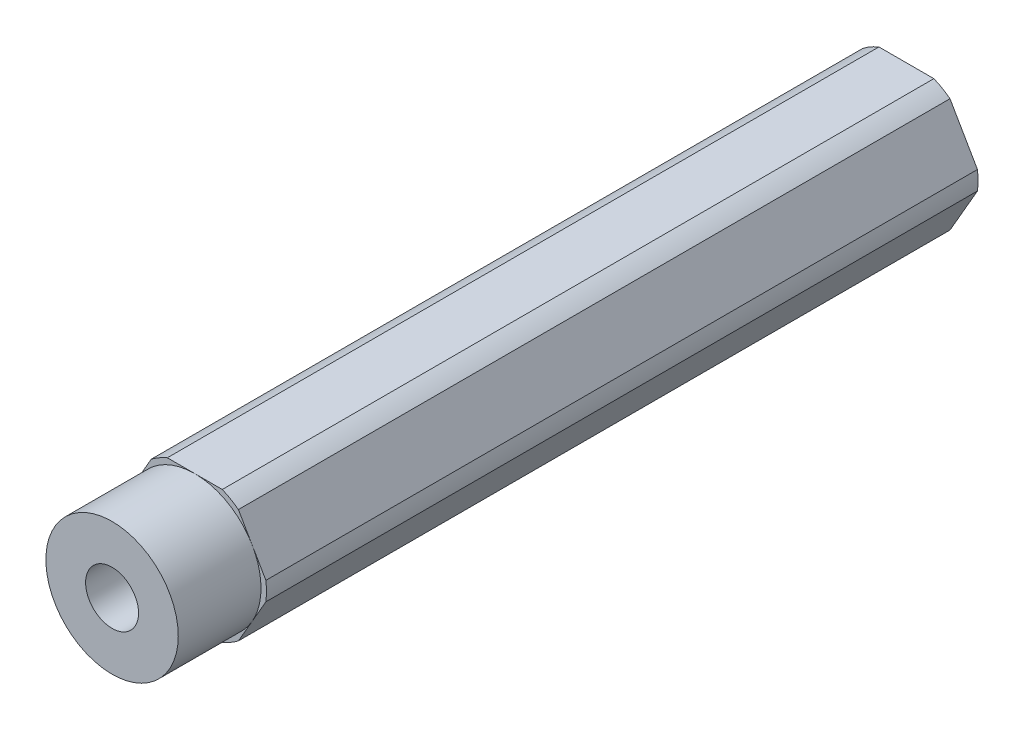
SolidWorks part; units mm, degrees
material "6061-T6 (SS)"
ref_plane "Front Plane" through (0, 0, 0) normal (0, 0, 1) x (1, 0, 0)
ref_plane "Top Plane" through (0, 0, 0) normal (0, 1, 0) x (1, 0, 0)
ref_plane "Right Plane" through (0, 0, 0) normal (1, 0, 0) x (0, 0, -1)
sketch "Sketch1" plane through (0, 0, 0) normal (0, 0, 1) x (1, 0, 0)
  line L1 (4.1818, -5.457) -> (6.8168, -0.893)
  line L2 (6.8168, 0.893) -> (4.1818, 5.457)
  line L3 (2.635, 6.35) -> (-2.635, 6.35)
  line L4 (-4.1818, 5.457) -> (-6.8168, 0.893)
  line L5 (-6.8168, -0.893) -> (-4.1818, -5.457)
  line L6 (-2.635, -6.35) -> (2.635, -6.35)
  circle A0 centre (0, 0) radius 6.35 construction
  arc A1 (-4.1818, -5.457) -> (-2.635, -6.35) centre (0, 0) ccw
  arc A2 (2.635, -6.35) -> (4.1818, -5.457) centre (0, 0) ccw
  arc A3 (6.8168, -0.893) -> (6.8168, 0.893) centre (0, 0) ccw
  arc A4 (4.1818, 5.457) -> (2.635, 6.35) centre (0, 0) ccw
  arc A5 (-2.635, 6.35) -> (-4.1818, 5.457) centre (0, 0) ccw
  arc A6 (-6.8168, 0.893) -> (-6.8168, -0.893) centre (0, 0) ccw
  circle A7 centre (0, 0) radius 2.54
  dimension "D1" = 12.7
  dimension "D2" = 13.75
  dimension "D3" = 5.08
extrude "Boss-Extrude1" add sketch "Sketch1" along normal blind 76.2
sketch "Sketch2" plane through (0, 0, 76.2) normal (0, 0, 1) x (1, 0, 0)
  circle A0 centre (0, 0) radius 6.35
  dimension "D1" = 12.7
extrude "Cut-Extrude1" cut sketch "Sketch2" against normal blind 7.9375 flip side to cut
